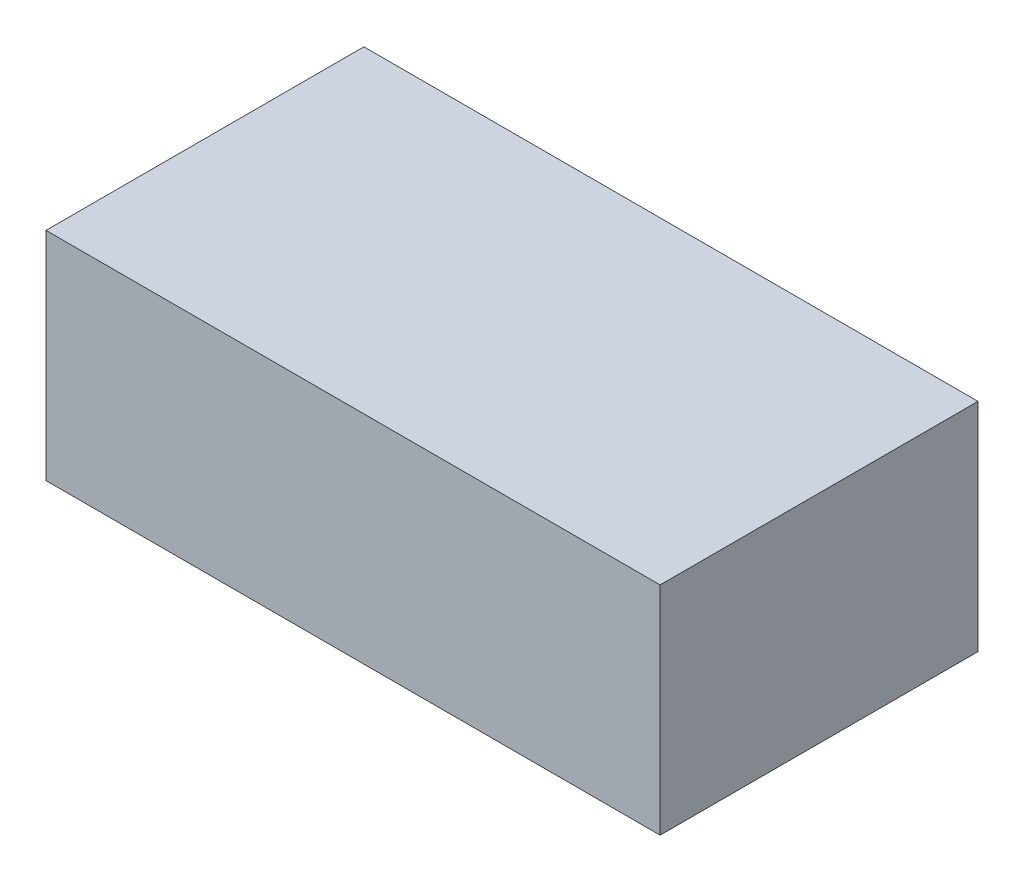
SolidWorks part; units mm, degrees
ref_plane "Front Plane" through (0, 0, 0) normal (0, 0, 1) x (1, 0, 0)
ref_plane "Top Plane" through (0, 0, 0) normal (0, 1, 0) x (1, 0, 0)
ref_plane "Right Plane" through (0, 0, 0) normal (1, 0, 0) x (0, 0, -1)
sketch "Sketch1" plane through (0, 0, 0) normal (0, 1, 0) x (1, 0, 0)
  line L1 (0, 0) -> (85, 0)
  line L2 (0, 0) -> (0, 44)
  line L3 (0, 44) -> (85, 44)
  line L4 (85, 0) -> (85, 44)
  dimension "D1" = 85
  dimension "D2" = 44
extrude "Boss-Extrude1" add sketch "Sketch1" along normal blind 30
